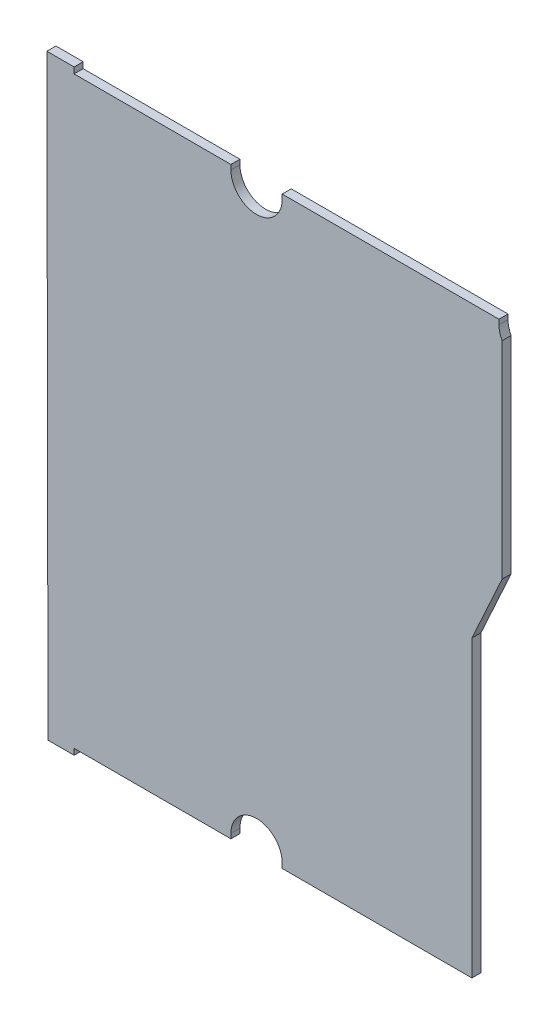
SolidWorks part; units mm, degrees
ref_plane "Front Plane" through (0, 0, 0) normal (0, 0, 1) x (1, 0, 0)
ref_plane "Top Plane" through (0, 0, 0) normal (0, 1, 0) x (1, 0, 0)
ref_plane "Right Plane" through (0, 0, 0) normal (1, 0, 0) x (0, 0, -1)
sketch "Sketch1" plane through (0, 0, 0) normal (0, 0, 1) x (1, 0, 0)
  line L17 (-66.795, -49.425) -> (-66.9813, 49.425)
  line L18 (-66.9813, 49.425) -> (-62.4676, 49.425)
  line L19 (-62.4676, 49.425) -> (-62.4676, 48.425)
  line L20 (-62.4676, 48.425) -> (-36.4676, 48.425)
  line L21 (-66.795, -49.425) -> (-62.4676, -49.425)
  line L22 (-62.4676, -49.425) -> (-62.4676, -48.425)
  line L23 (-62.4676, -48.425) -> (-36.4676, -48.425)
  line L24 (-36.4676, -48.425) -> (-36.4676, -47.625)
  line L25 (-27.9624, 47.625) -> (-27.9624, 48.425)
  line L26 (7.9824, 48.425) -> (-27.9624, 48.425)
  line L27 (7.9824, 48.425) -> (7.9824, 47.625)
  line L28 (8.5, 45.5917) -> (8.5, 11.3447)
  line L29 (8.5, 11.3447) -> (3.5, 0.4014)
  line L30 (3.5, 0.4014) -> (3.5, -48.425)
  line L31 (3.5, -48.425) -> (-27.9624, -48.425)
  line L32 (-27.9624, -48.425) -> (-27.9624, -47.625)
  line L33 (-36.4676, 47.625) -> (-36.4676, 48.425)
  line L51 (-71.995, 48.925) -> (-71.995, -48.925) construction
  line L52 (-71.495, -49.425) -> (-62.4676, -49.425) construction
  line L53 (-62.4676, -49.425) -> (-62.4676, -48.425) construction
  line L54 (-62.4676, -48.425) -> (-36.4676, -48.425) construction
  line L55 (-36.4676, -48.425) -> (-36.4676, -47.625) construction
  line L56 (-27.9624, -47.625) -> (-27.9624, -48.425) construction
  line L57 (-27.9624, -48.425) -> (3.5, -48.425) construction
  line L58 (3.5, -48.425) -> (3.5, 0.4014) construction
  line L59 (3.5, 0.4014) -> (8.5, 11.3447) construction
  line L60 (8.5, 11.3447) -> (8.5, 45.5917) construction
  line L61 (7.9824, 47.625) -> (7.9824, 48.425) construction
  line L62 (7.9824, 48.425) -> (-27.9624, 48.425) construction
  line L63 (-27.9624, 48.425) -> (-27.9624, 47.625) construction
  line L64 (-36.4676, 47.625) -> (-36.4676, 48.425) construction
  line L65 (-36.4676, 48.425) -> (-62.4676, 48.425) construction
  line L66 (-62.4676, 48.425) -> (-62.4676, 49.425) construction
  line L67 (-62.4676, 49.425) -> (-71.495, 49.425) construction
  arc A5 (-36.4676, -47.625) -> (-27.9624, -47.625) centre (-32.215, -47.625) cw
  arc A6 (7.9824, 47.625) -> (8.5, 45.5917) centre (12.235, 47.625) ccw
  arc A7 (-36.4676, 47.625) -> (-27.9624, 47.625) centre (-32.215, 47.625) ccw
  arc A15 (-71.995, -48.925) -> (-71.495, -49.425) centre (-71.495, -48.925) ccw construction
  arc A16 (-27.9624, -47.625) -> (-36.4676, -47.625) centre (-32.215, -47.625) ccw construction
  arc A17 (7.9824, 47.625) -> (8.5, 45.5917) centre (12.235, 47.625) ccw construction
  arc A18 (-36.4676, 47.625) -> (-27.9624, 47.625) centre (-32.215, 47.625) ccw construction
  arc A19 (-71.495, 49.425) -> (-71.995, 48.925) centre (-71.495, 48.925) ccw construction
extrude "Boss-Extrude1" add sketch "Sketch1" along normal blind 1.5
